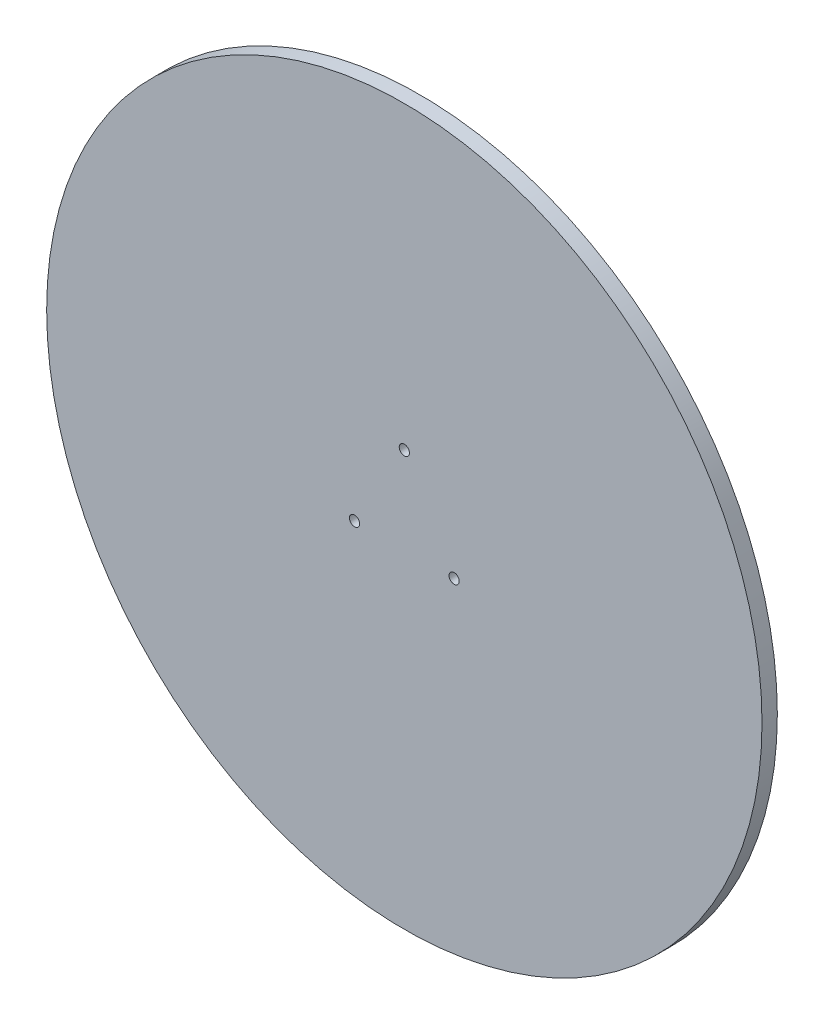
SolidWorks part; units mm, degrees
ref_plane "Front Plane" through (0, 0, 0) normal (0, 0, 1) x (1, 0, 0)
ref_plane "Top Plane" through (0, 0, 0) normal (0, 1, 0) x (1, 0, 0)
ref_plane "Right Plane" through (0, 0, 0) normal (1, 0, 0) x (0, 0, -1)
sketch "Sketch1" plane through (0, 0, 0) normal (0, 0, 1) x (1, 0, 0)
  line L0 (0, 0) -> (0, 22.5) construction
  circle A0 centre (0, 0) radius 140
  circle A1 centre (0, 22.5) radius 2
  circle A2 centre (19.4856, -11.25) radius 2
  circle A3 centre (-19.4856, -11.25) radius 2
  circle A4 centre (0, 0) radius 22.5 construction
  point P11 (0, 0)
  dimension "D1" = 280
  dimension "D3" = 4
  dimension "D4" = 45
  dimension "D2" = 3
extrude "Boss-Extrude1" add sketch "Sketch1" along normal blind 6
